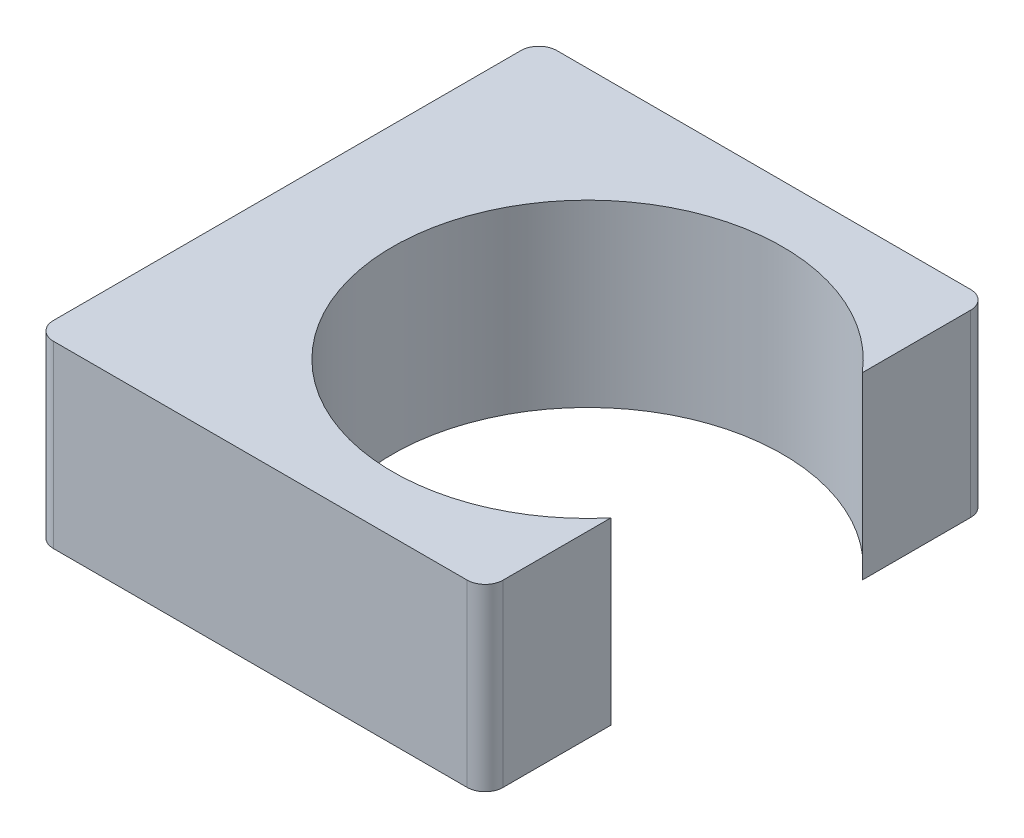
SolidWorks part; units mm, degrees
ref_plane "Front Plane" through (0, 0, 0) normal (0, 0, 1) x (1, 0, 0)
ref_plane "Top Plane" through (0, 0, 0) normal (0, 1, 0) x (1, 0, 0)
ref_plane "Right Plane" through (0, 0, 0) normal (1, 0, 0) x (0, 0, -1)
sketch "Sketch1" plane through (0, 0, 0) normal (0, 1, 0) x (1, 0, 0)
  line L0 (0, 17.78) -> (21.0737, 17.78)
  line L1 (0, -17.78) -> (21.0737, -17.78)
  line L2 (21.0737, 17.78) -> (21.0737, 33.1014)
  line L3 (18.5337, 35.6414) -> (-39.9905, 35.6414)
  line L4 (21.0737, -17.78) -> (21.0737, -33.0225)
  line L5 (18.5337, -35.5625) -> (-39.9905, -35.5625)
  line L6 (-42.5305, -33.0225) -> (-42.5305, 33.1014)
  circle A0 centre (0, 0) radius 17.78
  arc A1 (21.0737, 17.78) -> (21.0737, -17.78) centre (0, 0) ccw
  arc A2 (18.5337, 35.6414) -> (21.0737, 33.1014) centre (18.5337, 33.1014) cw
  arc A3 (21.0737, -33.0225) -> (18.5337, -35.5625) centre (18.5337, -33.0225) cw
  arc A4 (-42.5305, -33.0225) -> (-39.9905, -35.5625) centre (-39.9905, -33.0225) ccw
  arc A5 (-39.9905, 35.6414) -> (-42.5305, 33.1014) centre (-39.9905, 33.1014) ccw
  dimension "D1" = 35.56
  dimension "D2" = 2.54
extrude "Boss-Extrude1" add sketch "Sketch1" along normal blind 25.4 contours L3 A5 L6 A4 L5 A3 L4 A1 L2 A2
